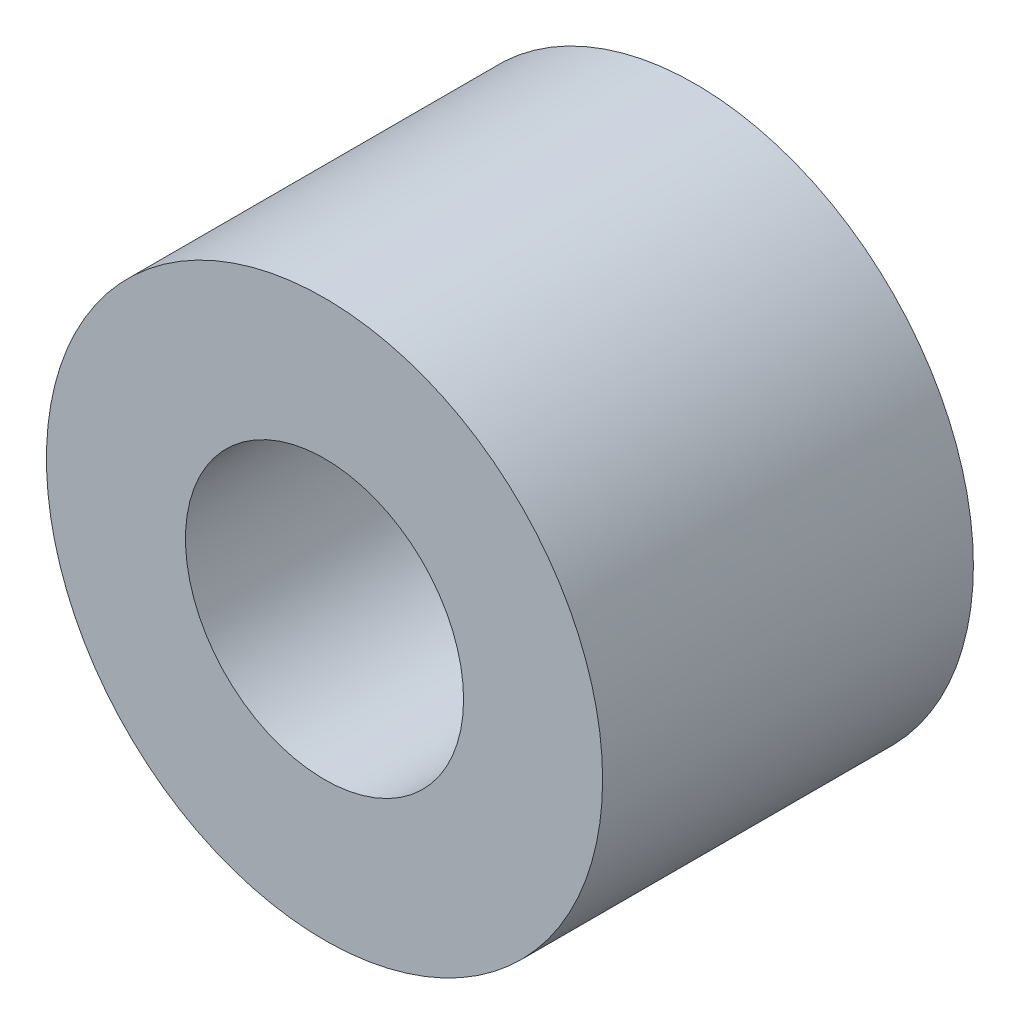
SolidWorks part; units mm, degrees
material "Beech"
ref_plane "Front Plane" through (0, 0, 0) normal (0, 0, 1) x (1, 0, 0)
ref_plane "Top Plane" through (0, 0, 0) normal (0, 1, 0) x (1, 0, 0)
ref_plane "Right Plane" through (0, 0, 0) normal (1, 0, 0) x (0, 0, -1)
sketch "Sketch1" plane through (0, 0, 0) normal (0, 0, 1) x (1, 0, 0)
  circle A0 centre (3, 3) radius 3
  circle A1 centre (3, 3) radius 1.5
extrude "Boss-Extrude1" add sketch "Sketch1" along normal blind 4
